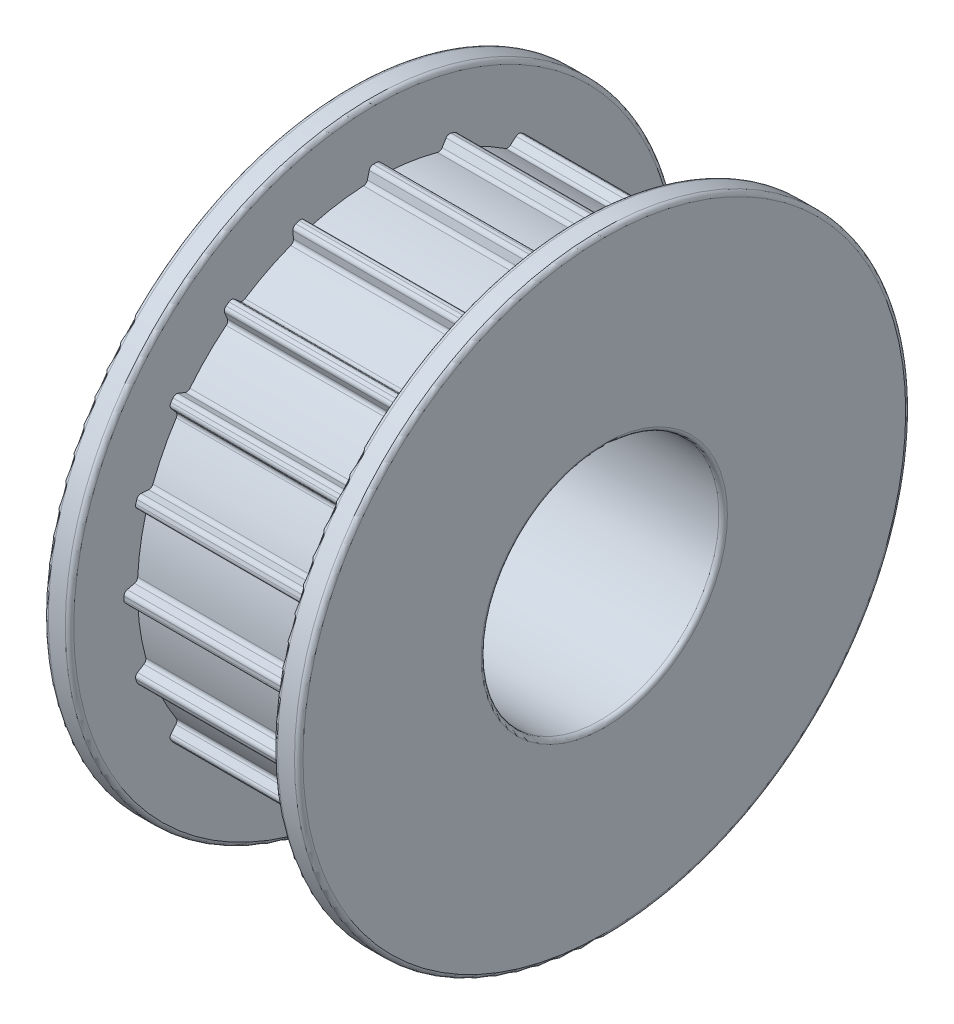
SolidWorks part; units mm, degrees
material "1060 Alloy"
ref_plane "Front Plane" through (0, 0, 0) normal (0, 0, 1) x (1, 0, 0)
ref_plane "Top Plane" through (0, 0, 0) normal (0, 1, 0) x (1, 0, 0)
ref_plane "Right Plane" through (0, 0, 0) normal (1, 0, 0) x (0, 0, -1)
sketch "Sketch1" plane through (0, 0, 0) normal (0, 0, 1) x (1, 0, 0)
  line L0 (-101.2063, 0) -> (4959.1107, 0) construction
  line L1 (0, -101.2063) -> (0, 4959.1107) construction
  line L2 (-7.5, 7) -> (7.5, 7)
  line L3 (7.5, 7) -> (7.5, 18)
  line L4 (7.5, 18) -> (6, 18)
  line L5 (6, 18) -> (6, 14)
  line L6 (6, 14) -> (-6, 14)
  line L7 (-7.5, 18) -> (-6, 18)
  line L8 (-6, 18) -> (-6, 14)
  line L9 (-7.5, 7) -> (-7.5, 18)
  point P4 (0, 14)
  point P15 (0, 7)
  dimension "D1" = 14
  dimension "D2" = 36
  dimension "D3" = 4
  dimension "D4" = 15
  dimension "D5" = 1.5
revolve "Revolve1" add sketch "Sketch1" angle 360 about L0
fillet "Fillet1" radius 0.25 6 edges at (-7.5, 0, 7) (7.5, 0, 7) (-7.5, 0, 18) (-6, 0, 18) (6, 0, 18) (7.5, 0, 18)
sketch "Sketch2" plane through (0, 0, 0) normal (1, 0, 0) x (0, 0, -1)
  line L0 (0, -1000) -> (0, 49000) construction
  line L1 (-1000.3535, 0) -> (48999.6465, 0) construction
  line L2 (0.3, 14.7911) -> (-0.3, 14.7911)
  line L3 (-0.3, 14.7911) -> (-0.5, 13.9911)
  line L4 (0.3, 14.7911) -> (0.5, 13.9911)
  line L5 (-0.5, 13.9911) -> (-0.5, 13.7911)
  line L6 (-0.5, 13.7911) -> (0.5, 13.7911)
  line L7 (0.5, 13.7911) -> (0.5, 13.9911)
  circle A0 centre (0, 0) radius 14 construction
  circle A1 centre (0, 0) radius 14 construction
  point P11 (0, 14.7911)
  dimension "D1" = 1
  dimension "D2" = 0.6
  dimension "D3" = 0.8
  dimension "D4" = 1
extrude "Boss-Extrude1" add sketch "Sketch2" along normal up to surface (6 mm away) and the other way up to surface (6 mm away) up to face at (6, 0, -17.75) other way up to face at (-6, 0, 17.75)
fillet "Fillet2" radius 0.25 4 edges at (0, 14.7911, -0.3) (0, 14.7911, 0.3) (0, 13.9911, -0.5) (0, 13.9911, 0.5)
pattern_circular "CirPattern1" count 20 over 360 about axis through (0, 0, 0) along (1, 0, 0) of "Fillet2", "Boss-Extrude1"
